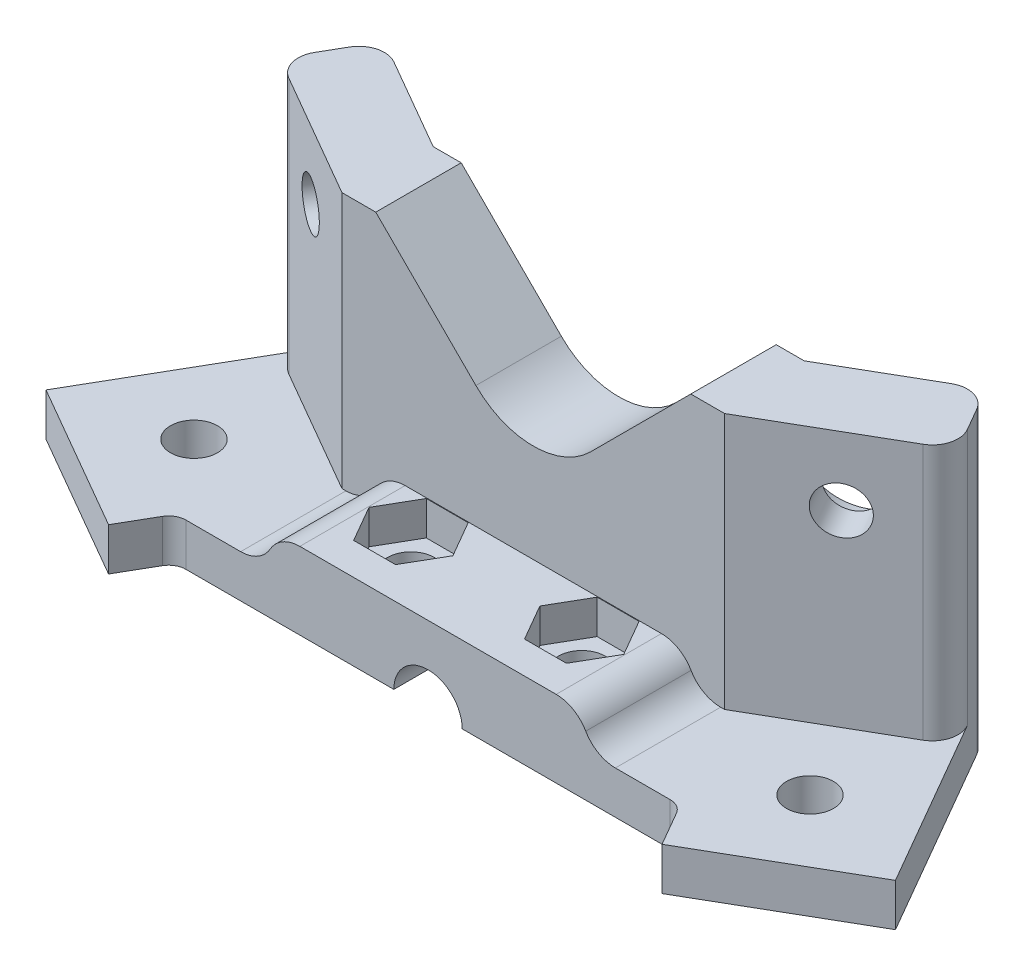
SolidWorks part; units mm, degrees
ref_plane "Front Plane" through (0, 0, 0) normal (0, 0, 1) x (1, 0, 0)
ref_plane "Top Plane" through (0, 0, 0) normal (0, 1, 0) x (1, 0, 0)
ref_plane "Right Plane" through (0, 0, 0) normal (1, 0, 0) x (0, 0, -1)
sketch "Sketch1" plane through (0, 0, 0) normal (0, 1, 0) x (1, 0, 0)
  line L0 (-39.7119, 0) -> (39.7119, 0)
  line L1 (39.7119, 0) -> (49.7119, -17.3205)
  line L2 (49.7119, -17.3205) -> (32.3914, -27.3205)
  line L3 (32.3914, -27.3205) -> (-32.3914, -27.3205) construction
  line L4 (-32.3914, -27.3205) -> (-49.7119, -17.3205)
  line L5 (-49.7119, -17.3205) -> (-39.7119, 0)
  line L6 (-36.0517, -13.6603) -> (36.0517, -13.6603) construction
  line L7 (0, -13.6603) -> (0, 0) construction
  line L8 (0, -13.6603) -> (0, -27.3205) construction
  line L9 (-32.3914, -27.3205) -> (-30.082, -23.3205)
  line L10 (-28.3499, -22.3205) -> (28.3499, -22.3205)
  line L11 (30.082, -23.3205) -> (32.3914, -27.3205)
  circle A0 centre (-36.0517, -13.6603) radius 2.75
  circle A1 centre (36.0517, -13.6603) radius 2.75
  arc A2 (28.3499, -22.3205) -> (30.082, -23.3205) centre (28.3499, -24.3205) cw
  arc A3 (-30.082, -23.3205) -> (-28.3499, -22.3205) centre (-28.3499, -24.3205) cw
  dimension "D3" = 5.5
  dimension "D9" = 2
  dimension "D1" = 60
  dimension "D2" = 60
  dimension "D4" = 72.1033
  dimension "D5" = 10
  dimension "D6" = 20
  dimension "D7" = 10
  dimension "D8" = 5
extrude "Boss-Extrude1" add sketch "Sketch1" along normal blind 5
sketch "Sketch2" plane through (0, 5, 0) normal (0, 1, 0) x (1, 0, 0)
  line L0 (-39.7119, 0) -> (-22.3914, -10)
  line L1 (-22.3914, -10) -> (22.3914, -10)
  line L2 (22.3914, -10) -> (39.7119, 0)
  line L3 (-39.7119, 0) -> (-49.7119, -17.3205) construction
  line L4 (49.7119, -17.3205) -> (39.7119, 0) construction
  line L5 (-21.7119, 0) -> (21.7119, 0)
  line L6 (-32.3914, -27.3205) -> (-22.3914, -10) construction
  line L7 (-39.7119, 0) -> (-36.7119, 5.1962)
  line L8 (39.7119, 0) -> (36.7119, 5.1962)
  line L9 (32.6138, 6.2942) -> (21.7119, 0)
  line L11 (-32.6138, 6.2942) -> (-21.7119, 0)
  arc A0 (36.7119, 5.1962) -> (32.6138, 6.2942) centre (34.1138, 3.6962) ccw
  arc A1 (-36.7119, 5.1962) -> (-32.6138, 6.2942) centre (-34.1138, 3.6962) cw
  point P12 (39.7119, 0)
  point P15 (-39.7119, 0)
  dimension "D1" = 3
  dimension "D2" = 9
extrude "Boss-Extrude2" add sketch "Sketch2" along normal blind 30 and the other way up to surface (5 mm away) other way up to face at (-36.0517, 0, 16.4103)
sketch "Sketch4" plane through (0, 0, 10) normal (0, 0, 1) x (1, 0, 0)
  line L0 (-15, 9) -> (15, 9)
  line L1 (-22.3914, 5) -> (22.3914, 5) construction
  line L3 (0, 9) -> (0, 0) construction
  line L4 (-21.9282, 5) -> (21.9282, 5)
  line L5 (-28.3499, 0) -> (28.3499, 0) construction
  arc A0 (-15, 9) -> (-18.4641, 7) centre (-15, 5) ccw
  arc A1 (-21.9282, 5) -> (-18.4641, 7) centre (-21.9282, 9) ccw
  arc A2 (18.4641, 7) -> (15, 9) centre (15, 5) ccw
  arc A3 (18.4641, 7) -> (21.9282, 5) centre (21.9282, 9) ccw
  dimension "D3" = 4
  dimension "D1" = 9
  dimension "D2" = 30
extrude "Boss-Extrude3" add sketch "Sketch4" along normal up to surface (12.3205 mm away) up to face at (0, 2.5, 22.3205)
sketch "Sketch5" plane through (0, 0, 0) normal (0, 0, -1) x (-1, 0, 0)
  line L0 (-21.7119, 0) -> (-21.7119, 35) construction
  line L1 (0, 30) -> (0, 0) construction
  line L2 (-21.7119, 0) -> (21.7119, 0) construction
  line L3 (-6.7175, 23.2825) -> (-18.435, 35)
  line L4 (-21.7119, 35) -> (21.7119, 35) construction
  line L5 (6.7175, 23.2825) -> (18.435, 35)
  line L6 (-18.435, 35) -> (18.435, 35)
  circle A0 centre (0, 0) radius 4
  arc A1 (-6.7175, 23.2825) -> (6.7175, 23.2825) centre (0, 30) ccw
  dimension "D2" = 19
  dimension "D3" = 8
  dimension "D4" = 45
  dimension "D1" = 30
extrude "Cut-Extrude1" cut sketch "Sketch5" against normal through all
sketch "Sketch7" plane through (9.928, 0, 17.1958) normal (0.5, 0, 0.866) x (0.866, 0, -0.5)
  line L0 (24.3915, 5) -> (24.3915, 0) construction
  line L2 (14.3915, 35) -> (34.3915, 35) construction
  circle A0 centre (24.3915, 27) radius 2.75
  dimension "D2" = 5.5
  dimension "D1" = 8
extrude "Cut-Extrude3" cut sketch "Sketch7" against normal through all
sketch "Sketch8" plane through (9.928, 0, 17.1958) normal (0.5, 0, 0.866) x (0.866, 0, -0.5)
  circle A0 centre (24.3915, 27) radius 6
  dimension "D1" = 12
extrude "Cut-Extrude4" cut sketch "Sketch8" against normal through all from offset 4 offset against normal yes
mirror "Mirror1" about plane through (0, 0, 0) normal (1, 0, 0) of "Cut-Extrude4", "Cut-Extrude3"
sketch "Sketch9" plane through (0, 9, 0) normal (0, 1, 0) x (1, 0, 0)
  line L0 (-15, -22.3205) -> (15, -22.3205) construction
  line L1 (-10, -14.3205) -> (10, -14.3205) construction
  line L2 (0, -14.3205) -> (0, -22.3205) construction
  line L3 (21.7119, 0) -> (4, 0) construction
  circle A0 centre (-10, -14.3205) radius 2.75
  circle A1 centre (10, -14.3205) radius 2.75
  dimension "D3" = 5.5
  dimension "D1" = 20
  dimension "D2" = 14.3205
extrude "Cut-Extrude5" cut sketch "Sketch9" against normal through all
sketch "Sketch10" plane through (0, 9, 0) normal (0, 1, 0) x (1, 0, 0)
  line L1 (-5.0925, -14.3205) -> (-7.5463, -10.0705)
  line L2 (-7.5463, -10.0705) -> (-12.4537, -10.0705)
  line L3 (-12.4537, -10.0705) -> (-14.9075, -14.3205)
  line L4 (-14.9075, -14.3205) -> (-12.4537, -18.5705)
  line L5 (-12.4537, -18.5705) -> (-7.5463, -18.5705)
  line L6 (-7.5463, -18.5705) -> (-5.0925, -14.3205)
  line L7 (5.0925, -14.3205) -> (7.5463, -18.5705)
  line L8 (7.5463, -18.5705) -> (12.4537, -18.5705)
  line L9 (12.4537, -18.5705) -> (14.9075, -14.3205)
  line L10 (14.9075, -14.3205) -> (12.4537, -10.0705)
  line L11 (12.4537, -10.0705) -> (7.5463, -10.0705)
  line L12 (7.5463, -10.0705) -> (5.0925, -14.3205)
  circle A0 centre (-10, -14.3205) radius 4.25 construction
  circle A1 centre (10, -14.3205) radius 4.25 construction
  dimension "D1" = 8.5
extrude "Cut-Extrude6" cut sketch "Sketch10" against normal offset from surface (4 mm away) 5 up to face at (-12.75, 0, 14.3205)
fillet "Fillet2" radius 3 2 edges at (39.7119, 20, 0) (-39.7119, 20, 0)
